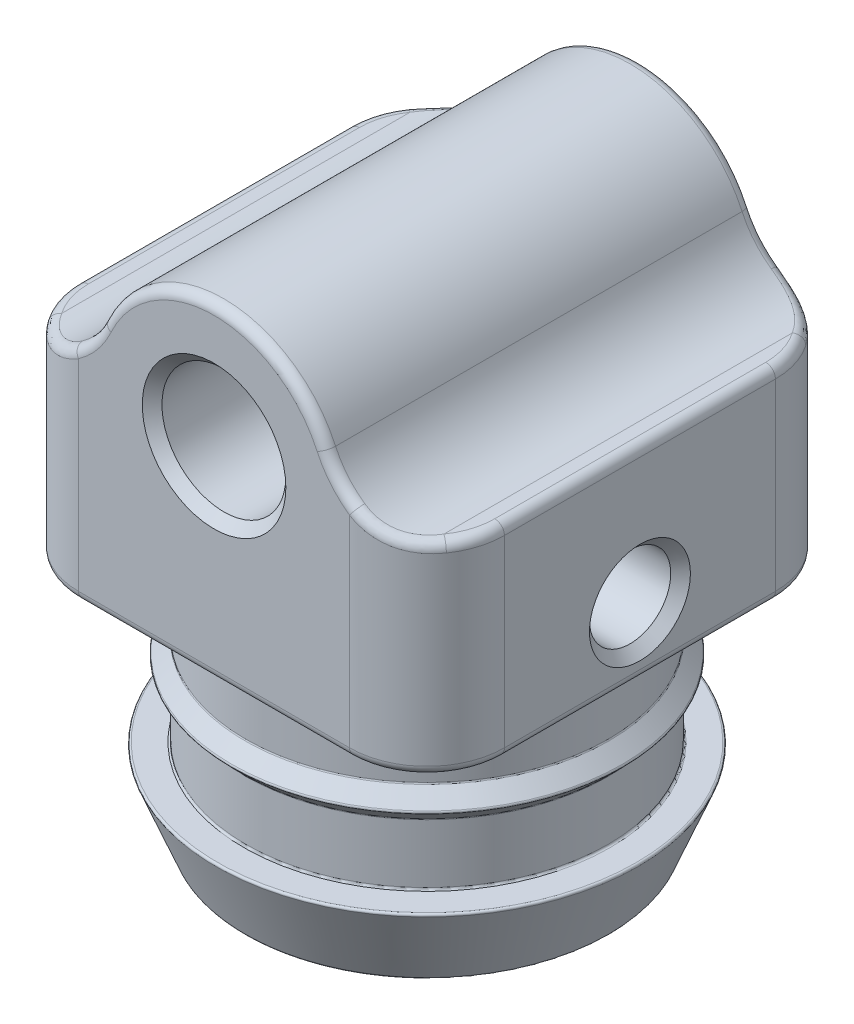
SolidWorks part; units mm, degrees
ref_plane "Front Plane" through (0, 0, 0) normal (0, 0, 1) x (1, 0, 0)
ref_plane "Top Plane" through (0, 0, 0) normal (0, 1, 0) x (1, 0, 0)
ref_plane "Right Plane" through (0, 0, 0) normal (1, 0, 0) x (0, 0, -1)
sketch "Sketch1" plane through (0, 0, 0) normal (0, 0, 1) x (1, 0, 0)
  line L3 (0, 0) -> (0, -10.5) construction
  line L4 (-11, 0) -> (-6.35, 0)
  line L5 (-11, 0) -> (-11, -10.5)
  line L6 (-11, -10.5) -> (11, -10.5)
  line L7 (11, 0) -> (11, -10.5)
  line L8 (6.35, 0) -> (11, 0)
  circle A0 centre (0, 0) radius 3.2
  arc A1 (6.35, 0) -> (-6.35, 0) centre (0, 0) ccw
  dimension "D1" = 6.4
  dimension "D2" = 12.7
  dimension "D4" = 22
  dimension "D5" = 10.5
extrude "Boss-Extrude1" add sketch "Sketch1" along normal mid plane 22
sketch3d "3DSketch1" plane through (0, 0, 0) normal (0, 0, 1) x (1, 0, 0)
  dimension "D1" = 12.7
sketch "Sketch2" plane through (0, 0, 0) normal (0, 0, 1) x (1, 0, 0)
  line L0 (0, 9.544) -> (0, -9.544) construction
  line L1 (0, -10) -> (9.365, -10)
  line L4 (0, -22.7) -> (9.365, -22.7)
  line L10 (0, -22.7) -> (0, -10)
  line L11 (9.365, -22.7) -> (10.9525, -18.7312)
  line L12 (10.9525, -18.7312) -> (9.365, -18.7312)
  line L13 (9.365, -18.7312) -> (9.365, -15.5562)
  line L14 (9.365, -15.5562) -> (10.1587, -14.7625)
  line L15 (10.1587, -14.7625) -> (9.365, -13.9687)
  line L16 (10.1587, -14.7625) -> (9.365, -14.7625) construction
  line L17 (9.365, -13.9687) -> (9.365, -10)
  dimension "D1" = 18.73
  dimension "D2" = 12.7
  dimension "D3" = 1.5875
  dimension "D4" = 3.9688
  dimension "D5" = 0.7937
  dimension "D6" = 7.9375
  dimension "D7" = 10
revolve "Revolve1" add sketch "Sketch2" angle 360 about L0
sketch "Sketch3" plane through (0, -22.7, 0) normal (0, -1, 0) x (1, 0, 0)
  circle A0 centre (0, 0) radius 4
  dimension "D1" = 8
extrude "Cut-Extrude1" cut sketch "Sketch3" against normal blind 18 contours A0
hole_wizard "M5x0.8 Tapped Hole1" positions "Sketch4" profile "Sketch5" tap size "M5x0.8" standard "ANSI Metric"
sketch "Sketch4" plane through (11, 0, 0) normal (1, 0, 0) x (0, 0, -1)
  point P0 (0, -7)
  dimension "D1" = 7
cosmetic thread "Hole Thread1" parameters "D2"=5
sketch "Sketch5" plane through (11, -7, 0) normal (0, 1, 0) x (0, 0, -1)
  line L0 (0, 0) -> (0, 7)
  line L1 (0, 7) -> (2.1, 7)
  line L2 (2.1, 7) -> (2.1, 0)
  line L5 (2.1, 0) -> (0, 0)
  line L11 (0, -6.35) -> (0, 107.95) construction
  dimension "Thru Tap Drill Dia." = 4.2
  dimension "Thru Tap Drill Depth" = 7
fillet "Fillet3" radius 0.0992 10 edges at (-10.9525, -18.7312, 0) (-10.1587, -14.7625, 0) (4, -22.7, 0) (4, -4.7, 0) (3.9957, -9.0917, -0.1863) (-9.365, -22.7, 0) (-9.365, -10.5, 0) (-9.365, -15.5562, 0) (-9.365, -13.9688, 0) (-9.365, -18.7312, 0)
chamfer "Chamfer1" distance 0.508 angle 45 3 edges at (3.2, 0, -11) (3.2, 0, 11) (11, -7, -2.1)
fillet "Fillet7" radius 4.5 2 edges at (-6.35, 0, 0) (6.35, 0, 0)
fillet "Fillet6" radius 4 4 edges at (11, -5.25, -11) (-11, -5.25, -11) (-11, -5.25, 11) (11, -5.25, 11)
fillet "Fillet8" radius 0.5 24 edges at (-9.8284, -10.5, 9.8284) (-11, -10.5, 0) (-9.8284, -10.5, -9.8284) (0, -10.5, -11) (9.8284, -10.5, -9.8284) (11, -10.5, 0) (9.8284, -10.5, 9.8284) (10.7075, 0, 8.5015) (8.9278, 0.1004, 10.5048) (6.2987, 1.7659, 11) (0, 6.35, 11) (-6.2987, 1.7659, 11) (-8.0042, 0.4063, 10.8719) (-10.7075, 0, 8.5015) (-11, 0, 0) (-10.7075, 0, -8.5015) (-8.9278, 0.1004, -10.5048) (-6.2987, 1.7659, -11) (0, 6.35, -11) (6.2987, 1.7659, -11) (8.0042, 0.4063, -10.8719) (10.7075, 0, -8.5015) (0, -10.5, 11) (11, 0, 0)
